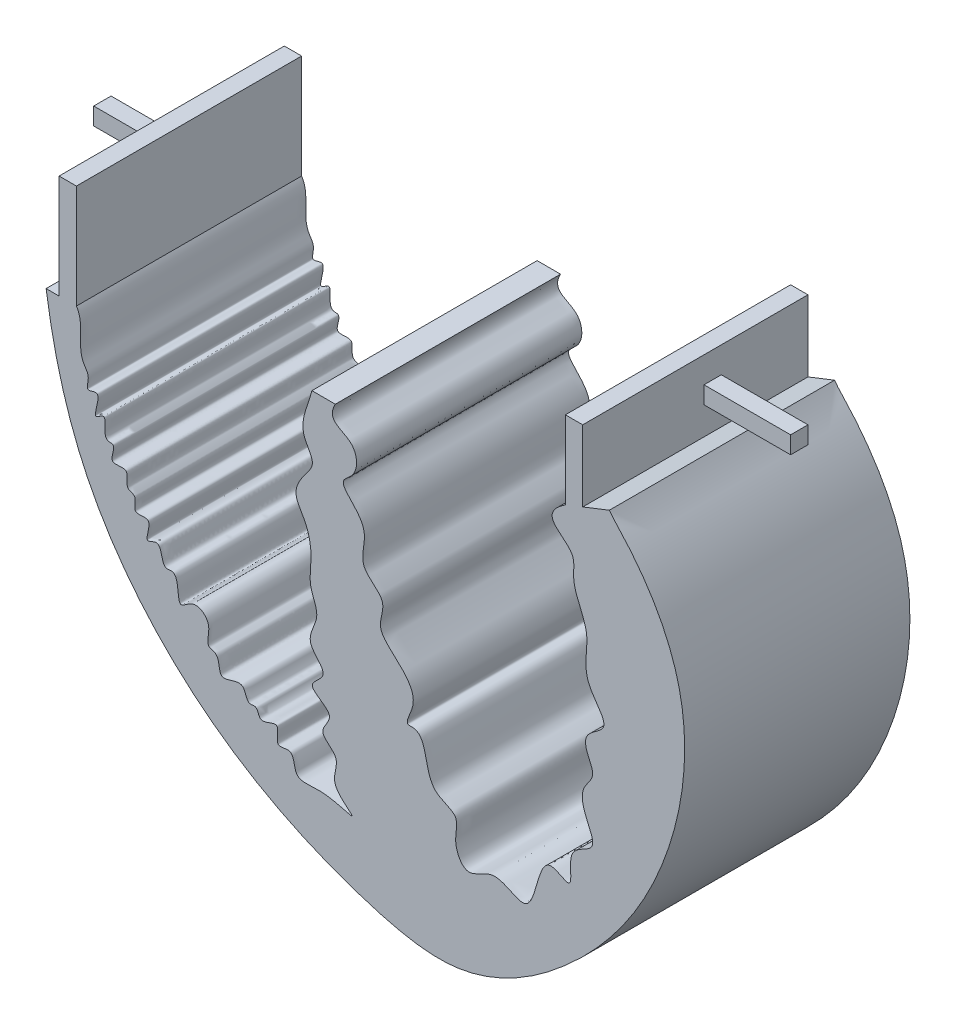
SolidWorks part; units mm, degrees
ref_plane "Front Plane" through (0, 0, 0) normal (0, 0, 1) x (1, 0, 0)
ref_plane "Top Plane" through (0, 0, 0) normal (0, 1, 0) x (1, 0, 0)
ref_plane "Right Plane" through (0, 0, 0) normal (1, 0, 0) x (0, 0, -1)
sketch "Sketch1" plane through (0, 0, 0) normal (0, 0, 1) x (1, 0, 0)
  line L0 (155.9186, 311.1659) -> (244.8186, 311.1659) construction
  line L1 (156.106, 303.3908) -> (158.009, 303.3908)
  line L2 (195.0745, 309.9128) -> (198.5106, 309.9128)
  line L3 (234.7829, 315.0012) -> (238.6852, 316.5378)
  line L6 (160.549, 303.3908) -> (160.549, 318.6308)
  line L7 (160.549, 318.6308) -> (158.009, 318.6308)
  line L8 (158.009, 303.3908) -> (158.009, 318.6308)
  line L10 (232.2429, 314.001) -> (232.2429, 325.431)
  line L11 (232.2429, 325.431) -> (234.7829, 325.431)
  line L12 (234.7829, 315.0012) -> (234.7829, 325.431)
  spline S0 degree 3 poles (156.106, 303.3908) (157.1041, 296.5504) (161.02, 280.597) (177.7965, 260.0912) (198.1255, 249.8913) (218.2382, 245.2961) (234.5508, 255.9018) (247.9377, 274.0446) (252.1422, 297.7029) (243.6089, 311.3426) (239.0608, 315.9795) (238.6852, 316.5378) knots 0.120047 0.120047 0.120047 0.120047 0.184834 0.273022 0.359649 0.397817 0.461195 0.526427 0.612455 0.666069 0.672634 0.672634 0.672634 0.672634
  spline S8 degree 3 poles (160.549, 303.3908) (161.8408, 301.4434) (160.251, 297.8527) (162.6391, 295.4166) (161.7217, 293.1072) (164.7814, 294.7704) (162.3957, 289.6722) (165.4406, 292.4559) (164.0989, 288.3343) (166.6095, 288.7205) (164.7842, 285.5003) (168.7304, 286.9203) (167.4626, 283.8855) (169.6592, 283.6799) (168.4106, 280.9056) (172.2444, 282.3419) (170.0615, 277.968) (173.2864, 280.1704) (172.8368, 276.2853) (175.8579, 277.2323) (174.9514, 271.6189) (177.8361, 274.9695) (180.8103, 272.7892) (179.2473, 269.7707) (181.7116, 269.544) (181.007, 265.5792) (185.3322, 268.6889) (185.4265, 265.2768) (187.1288, 265.9009) (187.2953, 263.4595) (190.8765, 266.1556) (189.3351, 261.7281) (192.5013, 263.1767) (192.3408, 258.8534) (196.4962, 260.4005) (203.0911, 257.7864) (197.119, 261.5072) (199.787, 265.2574) (195.4517, 267.1623) (199.2599, 270.408) (193.3874, 272.1819) (198.1997, 274.8268) (193.4131, 277.7216) (196.6943, 281.4719) (194.5068, 284.8449) (195.1555, 288.6932) (194.6409, 292.3986) (192.087, 295.6388) (193.6981, 298.4337) (195.8311, 300.8555) (192.5433, 304.4936) (194.6427, 307.9061) (195.0745, 309.9128) knots 0 0 0 0 0.051919 0.064008 0.075499 0.084669 0.10721 0.115506 0.136945 0.142204 0.158115 0.172986 0.189193 0.196237 0.210675 0.22436 0.243716 0.253596 0.275437 0.281725 0.310341 0.324821 0.346332 0.36683 0.372893 0.392675 0.415786 0.430902 0.436666 0.446704 0.464889 0.482308 0.494361 0.512123 0.54243 0.575248 0.60291 0.629688 0.651763 0.671434 0.699315 0.718217 0.745269 0.776014 0.801534 0.826229 0.862326 0.884845 0.910318 0.927809 0.949761 1 1 1 1
  spline S9 degree 3 poles (198.5106, 309.9128) (197.0234, 307.1856) (201.7454, 307.3627) (201.907, 302.3445) (198.9396, 300.6988) (201.4633, 298.2631) (203.4859, 295.6414) (201.506, 290.9408) (206.5209, 288.8119) (204.4036, 284.8406) (207.2595, 282.1873) (209.823, 279.8497) (210.1408, 277.0936) (208.5895, 274.4491) (212.3144, 274.8301) (210.8936, 267.774) (217.0509, 266.8776) (215.5773, 263.1231) (217.8681, 258.9503) (221.8086, 263.1629) (226.9755, 258.4948) (227.9499, 264.0668) (229.6673, 268.1122) (234.003, 264.6682) (231.8527, 271.1804) (237.2923, 271.9261) (235.0501, 275.9741) (234.2464, 279.1692) (236.961, 281.7183) (235.2524, 283.9545) (235.028, 286.833) (239.6404, 288.4967) (234.0689, 293.3828) (236.5231, 299.4388) (232.9463, 303.9822) (234.1362, 309.8891) (227.6718, 310.9116) (232.2429, 314.001) knots 0 0 0 0 0.040477 0.069913 0.084299 0.102582 0.130291 0.162598 0.194401 0.219561 0.241542 0.275577 0.294733 0.311599 0.314496 0.371031 0.396647 0.421679 0.446129 0.477509 0.513278 0.55109 0.573167 0.593986 0.625077 0.653561 0.678392 0.707285 0.726542 0.748879 0.761709 0.787968 0.825022 0.874319 0.923843 0.943137 1 1 1 1
  dimension "D1" = 88.9
  dimension "D2" = 2.54
  dimension "D3" = 15.24
  dimension "D4" = 2.54
  dimension "D5" = 11.43
  dimension "D6" = 10.4298
extrude "Boss-Extrude1" add sketch "Sketch1" along normal blind 33.02
sketch "Sketch2" plane through (158.009, 0, 0) normal (-1, 0, 0) x (0, 0, 1)
  line L0 (33.02, 318.6308) -> (33.02, 303.3908) construction
  line L1 (12.7, 312.2808) -> (15.24, 312.2808)
  line L2 (12.7, 312.2808) -> (12.7, 309.7408)
  line L3 (12.7, 309.7408) -> (15.24, 309.7408)
  line L4 (15.24, 312.2808) -> (15.24, 309.7408)
  line L5 (33.02, 318.6308) -> (0, 318.6308) construction
  dimension "D1" = 2.54
  dimension "D2" = 2.54
  dimension "D3" = 17.78
  dimension "D4" = 6.35
extrude "Boss-Extrude2" add sketch "Sketch2" along normal blind 12.7
sketch "Sketch3" plane through (234.7829, 0, 0) normal (1, 0, 0) x (0, 0, -1)
  line L0 (-33.02, 325.431) -> (0, 325.431) construction
  line L1 (-15.24, 321.621) -> (-12.7, 321.621)
  line L2 (-15.24, 321.621) -> (-15.24, 319.081)
  line L3 (-15.24, 319.081) -> (-12.7, 319.081)
  line L4 (-12.7, 321.621) -> (-12.7, 319.081)
  line L5 (-33.02, 315.0012) -> (-33.02, 325.431) construction
  point P4 (-13.97, 321.621)
  point P7 (-15.24, 320.351)
  dimension "D1" = 3.81
  dimension "D2" = 2.54
  dimension "D3" = 2.54
  dimension "D4" = 17.78
extrude "Boss-Extrude3" add sketch "Sketch3" along normal blind 12.7
